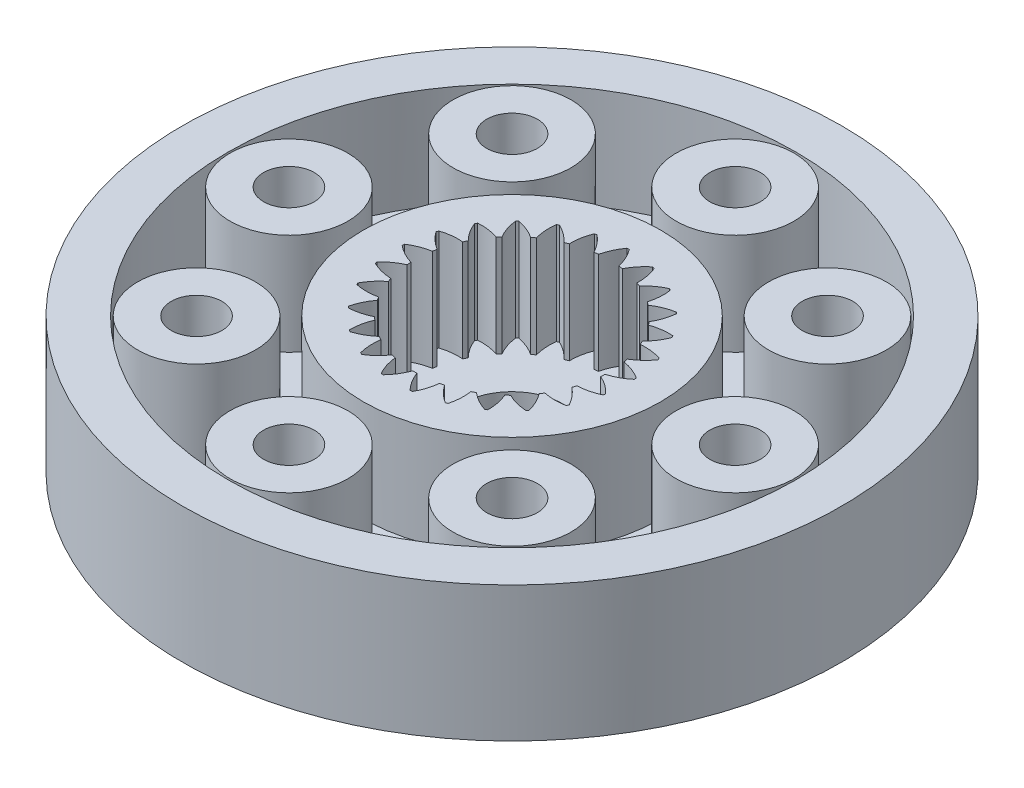
SolidWorks part; units mm, degrees
ref_plane "前视基准面" through (0, 0, 0) normal (0, 0, 1) x (1, 0, 0)
ref_plane "上视基准面" through (0, 0, 0) normal (0, 1, 0) x (1, 0, 0)
ref_plane "右视基准面" through (0, 0, 0) normal (1, 0, 0) x (0, 0, -1)
sketch "草图1" plane through (0, 0, 0) normal (0, 1, 0) x (1, 0, 0)
  circle A0 centre (0.3947, -0.592) radius 9.75
  arc A1 (-0.0261, 2.2521) -> (-0.4282, 2.7466) centre (-1.4141, 1.5344) ccw
  arc A2 (0.0949, 2.2673) -> (-0.0261, 2.2521) centre (0.3947, -0.592) ccw
  arc A3 (0.3614, 2.8463) -> (0.0949, 2.2673) centre (1.6177, 1.9174) ccw
  arc A4 (0.4279, 2.8463) -> (0.3614, 2.8463) centre (0.3947, -0.592) ccw
  arc A5 (0.6944, 2.2673) -> (0.4279, 2.8463) centre (-0.8284, 1.9174) ccw
  arc A6 (0.8154, 2.2521) -> (0.6944, 2.2673) centre (0.3947, -0.592) ccw
  arc A7 (1.2175, 2.7466) -> (0.8154, 2.2521) centre (2.2034, 1.5344) ccw
  arc A8 (1.282, 2.73) -> (1.2175, 2.7466) centre (0.3947, -0.592) ccw
  arc A9 (1.3961, 2.103) -> (1.282, 2.73) centre (-0.1659, 2.1427) ccw
  arc A10 (1.5095, 2.0581) -> (1.3961, 2.103) centre (0.3947, -0.592) ccw
  arc A11 (2.0219, 2.4371) -> (1.5095, 2.0581) centre (2.6754, 1.0178) ccw
  arc A12 (2.0803, 2.405) -> (2.0219, 2.4371) centre (0.3947, -0.592) ccw
  arc A13 (2.0348, 1.7693) -> (2.0803, 2.405) centre (0.5318, 2.1962) ccw
  arc A14 (2.1335, 1.6976) -> (2.0348, 1.7693) centre (0.3947, -0.592) ccw
  arc A15 (2.7241, 1.9372) -> (2.1335, 1.6976) centre (3.004, 0.4) ccw
  arc A16 (2.7726, 1.8917) -> (2.7241, 1.9372) centre (0.3947, -0.592) ccw
  arc A17 (2.5705, 1.2872) -> (2.7726, 1.8917) centre (1.2209, 2.0745) ccw
  arc A18 (2.6483, 1.1932) -> (2.5705, 1.2872) centre (0.3947, -0.592) ccw
  arc A19 (3.2799, 1.2785) -> (2.6483, 1.1932) centre (3.1688, -0.2801) ccw
  arc A20 (3.3156, 1.2223) -> (3.2799, 1.2785) centre (0.3947, -0.592) ccw
  arc A21 (2.9695, 0.687) -> (3.3156, 1.2223) centre (1.858, 1.7853) ccw
  arc A22 (3.0214, 0.5766) -> (2.9695, 0.687) centre (0.3947, -0.592) ccw
  arc A23 (3.6544, 0.5022) -> (3.0214, 0.5766) centre (3.1592, -0.9798) ccw
  arc A24 (3.675, 0.4389) -> (3.6544, 0.5022) centre (0.3947, -0.592) ccw
  arc A25 (3.2067, 0.0065) -> (3.675, 0.4389) centre (2.4033, 1.3467) ccw
  arc A26 (3.2295, -0.1133) -> (3.2067, 0.0065) centre (0.3947, -0.592) ccw
  arc A27 (3.8241, -0.3429) -> (3.2295, -0.1133) centre (2.9759, -1.6551) ccw
  arc A28 (3.8283, -0.4093) -> (3.8241, -0.3429) centre (0.3947, -0.592) ccw
  arc A29 (3.2672, -0.7116) -> (3.8283, -0.4093) centre (2.8223, 0.7862) ccw
  arc A30 (3.2595, -0.8334) -> (3.2672, -0.7116) centre (0.3947, -0.592) ccw
  arc A31 (3.7783, -1.2036) -> (3.2595, -0.8334) centre (2.6304, -2.2636) ccw
  arc A32 (3.7659, -1.269) -> (3.7783, -1.2036) centre (0.3947, -0.592) ccw
  arc A33 (3.1472, -1.4222) -> (3.7659, -1.269) centre (3.0888, 0.1392) ccw
  arc A34 (3.1095, -1.5382) -> (3.1472, -1.4222) centre (0.3947, -0.592) ccw
  arc A35 (3.5199, -2.0259) -> (3.1095, -1.5382) centre (2.1445, -2.7671) ccw
  arc A36 (3.4916, -2.0861) -> (3.5199, -2.0259) centre (0.3947, -0.592) ccw
  arc A37 (2.8542, -2.0806) -> (3.4916, -2.0861) centre (3.186, -0.5538) ccw
  arc A38 (2.7889, -2.1837) -> (2.8542, -2.0806) centre (0.3947, -0.592) ccw
  arc A39 (3.0652, -2.758) -> (2.7889, -2.1837) centre (1.5486, -3.1339) ccw
  arc A40 (3.0227, -2.8093) -> (3.0652, -2.758) centre (0.3947, -0.592) ccw
  arc A41 (2.4068, -2.6455) -> (3.0227, -2.8093) centre (3.1078, -1.2491) ccw
  arc A42 (2.3178, -2.7291) -> (2.4068, -2.6455) centre (0.3947, -0.592) ccw
  arc A43 (2.4426, -3.3541) -> (2.3178, -2.7291) centre (0.8801, -3.341) ccw
  arc A44 (2.3887, -3.3932) -> (2.4426, -3.3541) centre (0.3947, -0.592) ccw
  arc A45 (1.8329, -3.0814) -> (2.3887, -3.3932) centre (2.8591, -1.9032) ccw
  arc A46 (1.7259, -3.1402) -> (1.8329, -3.0814) centre (0.3947, -0.592) ccw
  arc A47 (1.6913, -3.7766) -> (1.7259, -3.1402) centre (0.1812, -3.3754) ccw
  arc A48 (1.6295, -3.8011) -> (1.6913, -3.7766) centre (0.3947, -0.592) ccw
  arc A49 (1.1686, -3.3609) -> (1.6295, -3.8011) centre (2.4556, -2.4749) ccw
  arc A50 (1.0504, -3.3912) -> (1.1686, -3.3609) centre (0.3947, -0.592) ccw
  arc A51 (0.8586, -3.999) -> (1.0504, -3.3912) centre (-0.5043, -3.2349) ccw
  arc A52 (0.7926, -4.0074) -> (0.8586, -3.999) centre (0.3947, -0.592) ccw
  arc A53 (0.4557, -3.4663) -> (0.7926, -4.0074) centre (1.9226, -2.9283) ccw
  arc A54 (0.3337, -3.4663) -> (0.4557, -3.4663) centre (0.3947, -0.592) ccw
  arc A55 (-0.0033, -4.0074) -> (0.3337, -3.4663) centre (-1.1333, -2.9283) ccw
  arc A56 (-0.0693, -3.999) -> (-0.0033, -4.0074) centre (0.3947, -0.592) ccw
  arc A57 (-0.2611, -3.3912) -> (-0.0693, -3.999) centre (1.2936, -3.2349) ccw
  arc A58 (-0.3793, -3.3609) -> (-0.2611, -3.3912) centre (0.3947, -0.592) ccw
  arc A59 (-0.8401, -3.8011) -> (-0.3793, -3.3609) centre (-1.6663, -2.4749) ccw
  arc A60 (-0.902, -3.7766) -> (-0.8401, -3.8011) centre (0.3947, -0.592) ccw
  arc A61 (-0.9366, -3.1402) -> (-0.902, -3.7766) centre (0.6081, -3.3754) ccw
  arc A62 (-1.0435, -3.0814) -> (-0.9366, -3.1402) centre (0.3947, -0.592) ccw
  arc A63 (-1.5994, -3.3932) -> (-1.0435, -3.0814) centre (-2.0698, -1.9032) ccw
  arc A64 (-1.6533, -3.3541) -> (-1.5994, -3.3932) centre (0.3947, -0.592) ccw
  arc A65 (-1.5285, -2.7291) -> (-1.6533, -3.3541) centre (-0.0908, -3.341) ccw
  arc A66 (-1.6174, -2.6455) -> (-1.5285, -2.7291) centre (0.3947, -0.592) ccw
  arc A67 (-2.2334, -2.8093) -> (-1.6174, -2.6455) centre (-2.3185, -1.2491) ccw
  arc A68 (-2.2758, -2.758) -> (-2.2334, -2.8093) centre (0.3947, -0.592) ccw
  arc A69 (-1.9995, -2.1837) -> (-2.2758, -2.758) centre (-0.7592, -3.1339) ccw
  arc A70 (-2.0649, -2.0806) -> (-1.9995, -2.1837) centre (0.3947, -0.592) ccw
  arc A71 (-2.7023, -2.0861) -> (-2.0649, -2.0806) centre (-2.3967, -0.5538) ccw
  arc A72 (-2.7306, -2.0259) -> (-2.7023, -2.0861) centre (0.3947, -0.592) ccw
  arc A73 (-2.3202, -1.5382) -> (-2.7306, -2.0259) centre (-1.3551, -2.7671) ccw
  arc A74 (-2.3579, -1.4222) -> (-2.3202, -1.5382) centre (0.3947, -0.592) ccw
  arc A75 (-2.9765, -1.269) -> (-2.3579, -1.4222) centre (-2.2995, 0.1392) ccw
  arc A76 (-2.989, -1.2036) -> (-2.9765, -1.269) centre (0.3947, -0.592) ccw
  arc A77 (-2.4702, -0.8334) -> (-2.989, -1.2036) centre (-1.8411, -2.2636) ccw
  arc A78 (-2.4779, -0.7116) -> (-2.4702, -0.8334) centre (0.3947, -0.592) ccw
  arc A79 (-3.039, -0.4093) -> (-2.4779, -0.7116) centre (-2.033, 0.7862) ccw
  arc A80 (-3.0348, -0.3429) -> (-3.039, -0.4093) centre (0.3947, -0.592) ccw
  arc A81 (-2.4402, -0.1133) -> (-3.0348, -0.3429) centre (-2.1866, -1.6551) ccw
  arc A82 (-2.4173, 0.0065) -> (-2.4402, -0.1133) centre (0.3947, -0.592) ccw
  arc A83 (-2.8857, 0.4389) -> (-2.4173, 0.0065) centre (-1.6139, 1.3467) ccw
  arc A84 (-2.8651, 0.5022) -> (-2.8857, 0.4389) centre (0.3947, -0.592) ccw
  arc A85 (-2.2321, 0.5766) -> (-2.8651, 0.5022) centre (-2.3699, -0.9798) ccw
  arc A86 (-2.1802, 0.687) -> (-2.2321, 0.5766) centre (0.3947, -0.592) ccw
  arc A87 (-2.5263, 1.2223) -> (-2.1802, 0.687) centre (-1.0687, 1.7853) ccw
  arc A88 (-2.4906, 1.2785) -> (-2.5263, 1.2223) centre (0.3947, -0.592) ccw
  arc A89 (-1.859, 1.1932) -> (-2.4906, 1.2785) centre (-2.3794, -0.2801) ccw
  arc A90 (-1.7812, 1.2872) -> (-1.859, 1.1932) centre (0.3947, -0.592) ccw
  arc A91 (-1.9833, 1.8917) -> (-1.7812, 1.2872) centre (-0.4315, 2.0745) ccw
  arc A92 (-1.9348, 1.9372) -> (-1.9833, 1.8917) centre (0.3947, -0.592) ccw
  arc A93 (-1.3442, 1.6976) -> (-1.9348, 1.9372) centre (-2.2147, 0.4) ccw
  arc A94 (-1.2455, 1.7693) -> (-1.3442, 1.6976) centre (0.3947, -0.592) ccw
  arc A95 (-1.2909, 2.405) -> (-1.2455, 1.7693) centre (0.2576, 2.1962) ccw
  arc A96 (-1.2326, 2.4371) -> (-1.2909, 2.405) centre (0.3947, -0.592) ccw
  arc A97 (-0.7202, 2.0581) -> (-1.2326, 2.4371) centre (-1.886, 1.0178) ccw
  arc A98 (-0.6067, 2.103) -> (-0.7202, 2.0581) centre (0.3947, -0.592) ccw
  arc A99 (-0.4927, 2.73) -> (-0.6067, 2.103) centre (0.9553, 2.1427) ccw
  arc A100 (-0.4282, 2.7466) -> (-0.4927, 2.73) centre (0.3947, -0.592) ccw
extrude "凸台-拉伸1" add sketch "草图1" along normal blind 3
ref_plane "基准面1" through (0, 0, 0) normal (0, -1, 0) x (-1, 0, 0)
sketch "草图2" plane through (0, 0, 0) normal (0, -1, 0) x (-1, 0, 0)
  line L0 (10.4941, -0.7442) -> (4.2859, -0.7442) construction
  circle A0 centre (-0.3947, -0.592) radius 9.75
extrude "凸台-拉伸2" add sketch "草图2" along normal blind 1
ref_plane "基准面2" through (0, 0, 0) normal (0, 1, 0) x (1, 0, 0)
sketch "草图4" plane through (0, 0, 0) normal (0, 1, 0) x (1, 0, 0)
  circle A0 centre (0.3947, -0.592) radius 1.5
extrude "切除-拉伸4" cut sketch "草图4" against normal blind 1
ref_plane "基准面3" through (0, 3, 0) normal (0, 1, 0) x (1, 0, 0)
sketch "草图5" plane through (0, 0, 0) normal (0, -1, 0) x (-1, 0, 0)
  circle A0 centre (-0.3947, -0.592) radius 4.4
  circle A1 centre (-0.3947, -0.592) radius 8.4
extrude "切除-拉伸5" cut sketch "草图5" against normal blind 10
sketch "草图6" plane through (0, 0, 0) normal (0, -1, 0) x (-1, 0, 0)
  line L0 (-0.3947, -0.592) -> (-0.3947, 7.808) construction
  circle A0 centre (-0.3947, -0.592) radius 6.6 construction
  circle A1 centre (-0.3947, -0.592) radius 8.4 construction
  circle A2 centre (-0.3947, 6.008) radius 0.75
  circle A3 centre (4.2722, 4.0749) radius 0.75
  circle A4 centre (6.2053, -0.592) radius 0.75
  circle A5 centre (4.2722, -5.2589) radius 0.75
  circle A6 centre (-0.3947, -7.192) radius 0.75
  circle A7 centre (-5.0616, -5.2589) radius 0.75
  circle A8 centre (-6.9947, -0.592) radius 0.75
  circle A9 centre (-5.0616, 4.0749) radius 0.75
  circle A10 centre (-0.3947, 6.008) radius 1.7445
  circle A11 centre (4.2722, 4.0749) radius 1.7445
  circle A12 centre (6.2053, -0.592) radius 1.7445
  circle A13 centre (4.2722, -5.2589) radius 1.7445
  circle A14 centre (-0.3947, -7.192) radius 1.7445
  circle A15 centre (-5.0616, -5.2589) radius 1.7445
  circle A16 centre (-6.9947, -0.592) radius 1.7445
  circle A17 centre (-5.0616, 4.0749) radius 1.7445
  point P26 (-0.3947, -0.592)
  point P42 (-0.3947, -0.592)
  dimension "D1" = 8
  dimension "D2" = 8
extrude "凸台-拉伸3" add sketch "草图6" against normal blind 3
ref_plane "基准面4" through (0, -1, 0) normal (0, -1, 0) x (-1, 0, 0)
sketch "草图7" plane through (0, -1, 0) normal (0, -1, 0) x (-1, 0, 0)
  circle A0 centre (-0.3947, 6.008) radius 0.75 construction
  circle A1 centre (-0.3947, -0.592) radius 1.5 construction
  circle A2 centre (-0.3947, 6.008) radius 0.75
  circle A3 centre (-0.3947, -0.592) radius 1.5
  circle A4 centre (4.2722, 4.0749) radius 0.75
  circle A5 centre (6.2053, -0.592) radius 0.75
  circle A6 centre (4.2722, -5.2589) radius 0.75
  circle A7 centre (-0.3947, -7.192) radius 0.75
  circle A8 centre (-5.0616, -5.2589) radius 0.75
  circle A9 centre (-6.9947, -0.592) radius 0.75
  circle A10 centre (-5.0616, 4.0749) radius 0.75
  point P23 (0, 0)
  point P24 (-0.3947, -0.592)
  dimension "D1" = 8
extrude "切除-拉伸6" cut sketch "草图7" against normal blind 3
